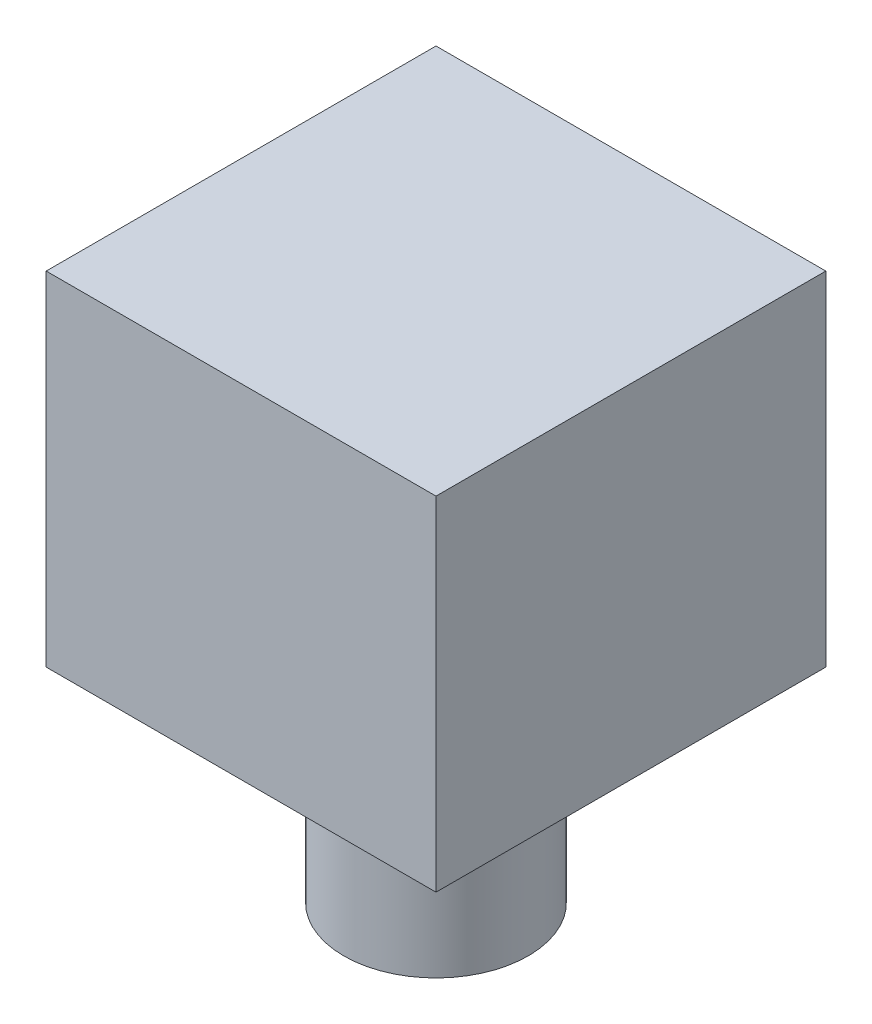
SolidWorks part; units mm, degrees
ref_plane "Front" through (0, 0, 0) normal (0, 0, 1) x (1, 0, 0)
ref_plane "Top" through (0, 0, 0) normal (0, 1, 0) x (1, 0, 0)
ref_plane "Right" through (0, 0, 0) normal (1, 0, 0) x (0, 0, -1)
sketch "Sketch3" plane through (0, 0, 0) normal (0, 1, 0) x (1, 0, 0)
  circle A0 centre (0, 0) radius 18.034
  dimension "D1" = 36.068
extrude "Boss-Extrude1" add sketch "Sketch3" along normal blind 39.878
sketch "Sketch4" plane through (0, 39.878, 0) normal (0, 1, 0) x (1, 0, 0)
  line L1 (-38.1, -38.1) -> (38.1, -38.1)
  line L2 (-38.1, -38.1) -> (-38.1, 38.1)
  line L3 (-38.1, 38.1) -> (38.1, 38.1)
  line L4 (38.1, -38.1) -> (38.1, 38.1)
  line L5 (-38.1, -38.1) -> (38.1, 38.1) construction
  line L6 (-38.1, 38.1) -> (38.1, -38.1) construction
  point P0 (0, 0)
  dimension "D1" = 76.2
  dimension "D2" = 76.2
extrude "Boss-Extrude2" add sketch "Sketch4" along normal blind 67.056
